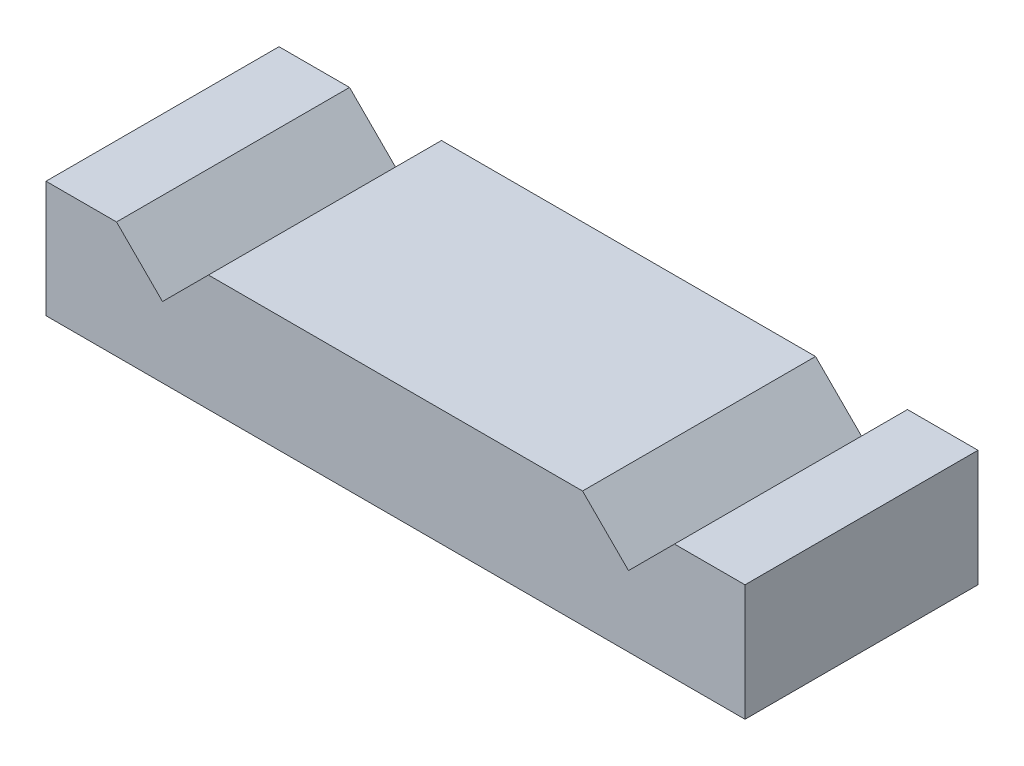
SolidWorks part; units mm, degrees
ref_plane "Front Plane" through (0, 0, 0) normal (0, 0, 1) x (1, 0, 0)
ref_plane "Top Plane" through (0, 0, 0) normal (0, 1, 0) x (1, 0, 0)
ref_plane "Right Plane" through (0, 0, 0) normal (1, 0, 0) x (0, 0, -1)
sketch "Sketch1" plane through (0, 0, 0) normal (0, 1, 0) x (1, 0, 0)
  line L1 (0, 0) -> (60, 0)
  line L2 (0, 0) -> (0, 20)
  line L3 (0, 20) -> (60, 20)
  line L4 (60, 0) -> (60, 20)
  dimension "D1" = 60
  dimension "D2" = 20
extrude "Boss-Extrude1" add sketch "Sketch1" along normal blind 10
sketch "Sketch2" plane through (0, 0, 0) normal (0, 0, 1) x (1, 0, 0)
  line L0 (0, 10) -> (60, 10) construction
  line L1 (10, 10) -> (50, 10)
  line L2 (10, 10) -> (10, 6.0548)
  line L3 (10, 6.0548) -> (50, 6.0548)
  line L4 (50, 10) -> (50, 6.0548)
  line L5 (0, 10) -> (0, 0) construction
  line L6 (60, 10) -> (60, 0) construction
  line L7 (30, 10) -> (30, 0) construction
  line L8 (10, 6.0548) -> (6.0548, 10)
  line L9 (10, 6.0548) -> (13.9452, 10)
  line L10 (0, 0) -> (60, 0) construction
  line L11 (6.0548, 10) -> (10, 13.9452)
  line L12 (13.9452, 10) -> (10, 13.9452)
  line L13 (53.9452, 10) -> (50, 13.9452)
  line L14 (46.0548, 10) -> (50, 13.9452)
  line L15 (50, 6.0548) -> (46.0548, 10)
  line L16 (50, 6.0548) -> (53.9452, 10)
  point P14 (0, 0)
  point P18 (0, 0)
  point P19 (0, 0)
  dimension "D1" = 10
  dimension "D2" = 10
  dimension "D3" = 6.0548
extrude "Cut-Extrude1" cut sketch "Sketch2" against normal through all contours L14 L6 L13 | L4 L16 L6 | L15 L4 L6 | L8 L9 L12 L11
